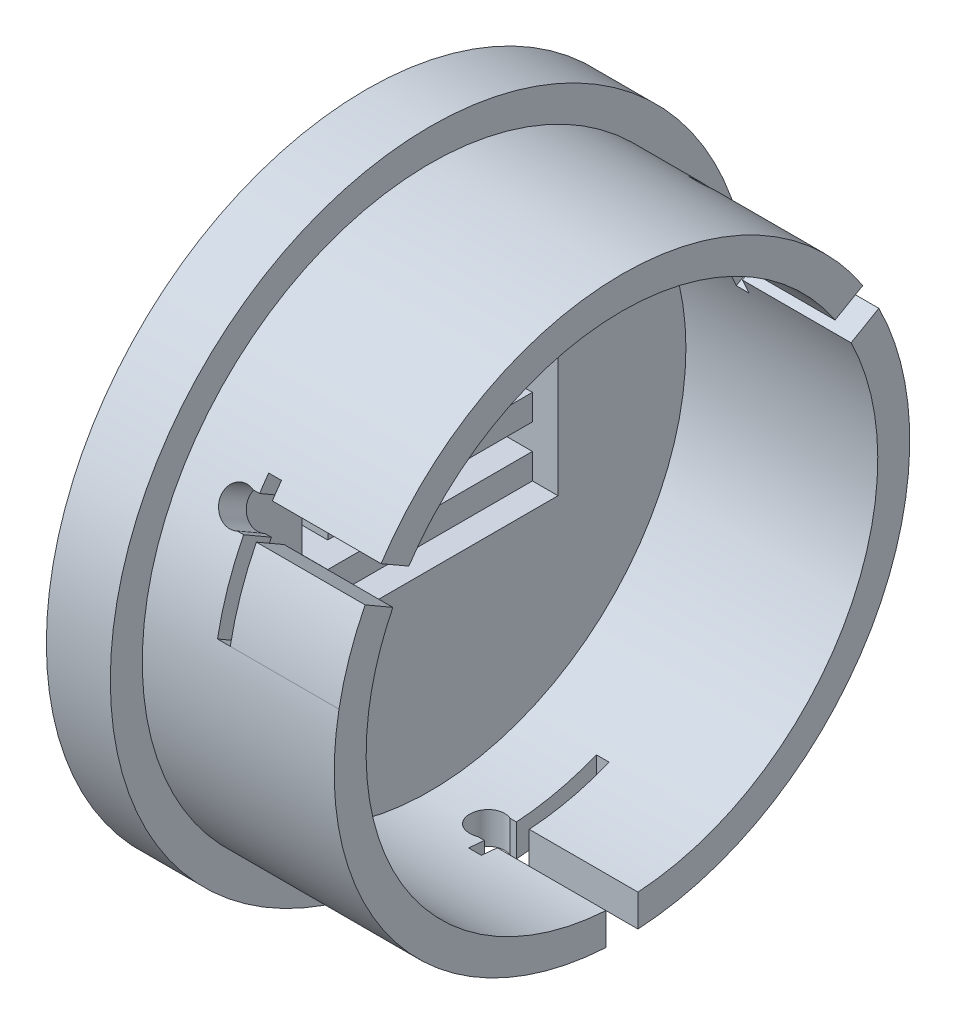
SolidWorks part; units mm, degrees
material "ABS"
ref_plane "Front Plane" through (0, 0, 0) normal (0, 0, 1) x (1, 0, 0)
ref_plane "Top Plane" through (0, 0, 0) normal (0, 1, 0) x (1, 0, 0)
ref_plane "Right Plane" through (0, 0, 0) normal (1, 0, 0) x (0, 0, -1)
sketch "Sketch1" plane through (0, 0, 0) normal (1, 0, 0) x (0, 0, -1)
  circle A0 centre (0, 0) radius 50
  dimension "D1" = 100
extrude "Boss-Extrude1" add sketch "Sketch1" along normal mid plane 10
sketch "Sketch2" plane through (5, 0, 0) normal (1, 0, 0) x (0, 0, -1)
  circle A0 centre (0, 0) radius 45
  circle A1 centre (0, 0) radius 40
  dimension "D1" = 90
  dimension "D2" = 80
extrude "Boss-Extrude2" add sketch "Sketch2" along normal blind 30
sketch "Sketch6" plane through (0, 0, 0) normal (0, 1, 0) x (1, 0, 0)
  line L0 (35, -45) -> (35, 45) construction
  line L1 (55, -2.5) -> (18, -2.5)
  line L3 (55, -2.5) -> (55, 2.5)
  line L4 (55, 2.5) -> (18, 2.5)
  line L5 (16, 2.375) -> (16, 15)
  line L6 (55, -2.5) -> (15, 2.5) construction
  line L7 (55, 2.5) -> (15, -2.5) construction
  line L9 (5, -45) -> (5, 45) construction
  line L10 (18, 2.125) -> (18, 15)
  line L11 (18, -5) -> (16, -5)
  line L12 (18, -5) -> (18, -2.5)
  line L13 (18, 15) -> (16, 15)
  line L14 (16, -5) -> (16, -2.375)
  line L15 (18, -5) -> (16, 15) construction
  line L16 (18, 15) -> (16, -5) construction
  line L17 (16, 2.5) -> (15, 2.5)
  line L18 (16, -2.5) -> (15, -2.5)
  line L19 (55, 0) -> (13.9248, 0)
  arc A4 (15, -2.5) -> (15, 2.5) centre (13.9248, 0) cw
  point P0 (35, 0)
  point P9 (114.9716, 26.261)
  point P10 (63.054, -41.0411)
  point P11 (17, 5)
  point P13 (33.6705, 1.4589)
  point P32 (13.9248, 0)
  dimension "D1" = 5
  dimension "D4" = 12
  dimension "D7" = 20
  dimension "D2" = 2.7214
  dimension "D5" = 2
  dimension "D6" = 20
  dimension "D3" = 21.0752
  dimension "D8" = 2.5
sketch "Sketch7" plane through (-5, 0, 0) normal (-1, 0, 0) x (0, 0, 1)
  circle A0 centre (0, 0) radius 37.5
  dimension "D1" = 75
extrude "Boss-Extrude5" add sketch "Sketch7" along normal blind 5
extrude "Cut-Extrude5" cut sketch "Sketch6" against normal through all
sketch "Sketch8" plane through (-10, 0, 0) normal (-1, 0, 0) x (0, 0, 1)
  line L0 (-16, 0) -> (16, 0) construction
  line L1 (20, -10) -> (-20, -10)
  line L2 (20, -10) -> (20, 10)
  line L3 (20, 10) -> (-20, 10)
  line L4 (-20, -10) -> (-20, 10)
  line L5 (20, -10) -> (-20, 10) construction
  line L6 (20, 10) -> (-20, -10) construction
  line L7 (-16, -2) -> (16, -2)
  line L8 (-16, 2) -> (16, 2)
  line L10 (16, 6) -> (-16, 6)
  line L11 (-16, -6) -> (-16, 6)
  line L12 (16, -6) -> (-16, -6)
  line L13 (16, -6) -> (16, 6)
  point P0 (0, 0)
  dimension "D1" = 40
  dimension "D2" = 20
  dimension "D3" = 2
  dimension "D4" = 4
  dimension "D5" = 2
extrude "Cut-Extrude4" cut sketch "Sketch8" against normal blind 40 contours L4 L1 L2 L3 L13 L12 L11 L10 | L7 L13 L8 L11
pattern_circular "CirPattern6" count 3 over 360 about axis through (0, 0, 0) along (1, 0, 0) of "Cut-Extrude5"
